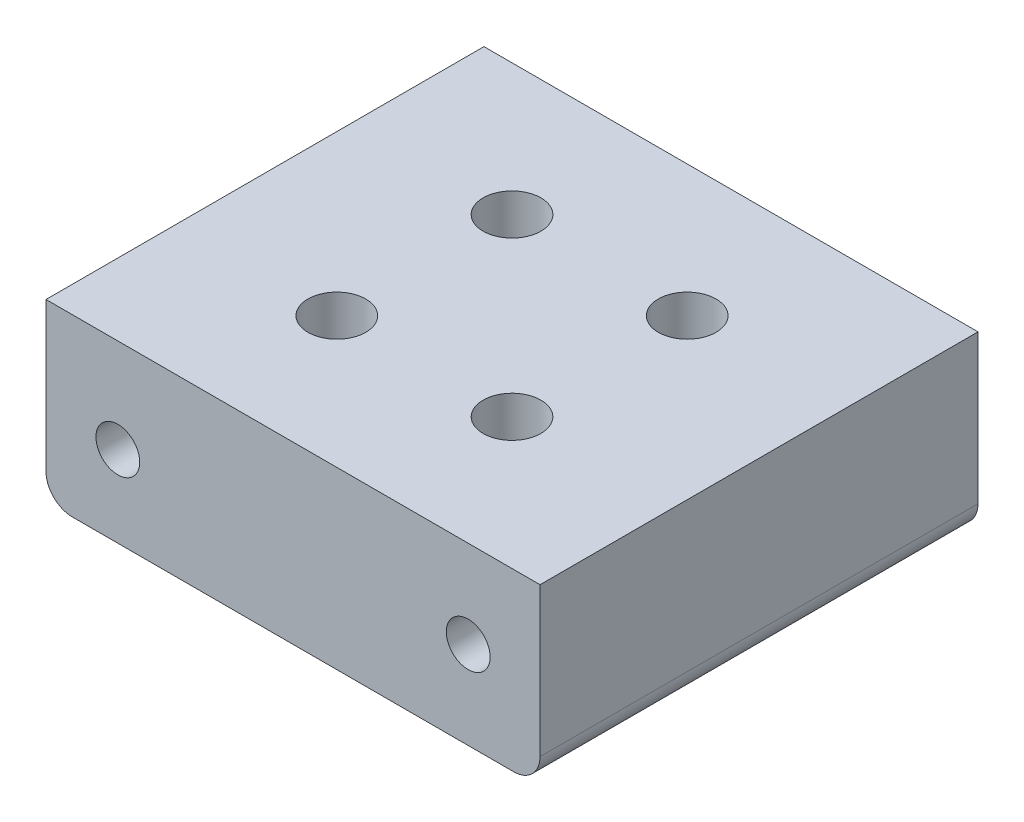
SolidWorks part; units mm, degrees
ref_plane "Front Plane" through (0, 0, 0) normal (0, 0, 1) x (1, 0, 0)
ref_plane "Top Plane" through (0, 0, 0) normal (0, 1, 0) x (1, 0, 0)
ref_plane "Right Plane" through (0, 0, 0) normal (1, 0, 0) x (0, 0, -1)
sketch "Sketch1" plane through (0, 0, 0) normal (0, 0, 1) x (1, 0, 0)
  line L5 (28.2, -17.5) -> (-28.2, -17.5)
  line L8 (-25.2, -37.5) -> (25.2, -37.5)
  line L9 (28.2, -34.5) -> (28.2, -17.5)
  line L11 (-28.2, -17.5) -> (-28.2, -34.5)
  arc A8 (25.2, -37.5) -> (28.2, -34.5) centre (25.2, -34.5) ccw
  arc A11 (-28.2, -34.5) -> (-25.2, -37.5) centre (-25.2, -34.5) ccw
extrude "Boss-Extrude1" add sketch "Sketch1" along normal blind 50
hole_wizard "Tap Drill for M6 Tap1" positions "Sketch2" profile "Sketch3" hole size "M6" standard "ISO" end condition through all
sketch "Sketch2" plane through (0, 0, 0) normal (0, 0, -1) x (-1, 0, 0)
  point P0 (-20, -27.5)
  point P2 (20, -28.2377)
sketch "Sketch3" plane through (20, -27.5, 0) normal (1, 0, 0) x (0, 1, 0)
  line L0 (0, 0) -> (0, 50)
  line L1 (0, 50) -> (2.5, 50)
  line L2 (2.5, 50) -> (2.5, 0)
  line L5 (2.5, 0) -> (0, 0)
  line L11 (0, -6.35) -> (0, 107.95) construction
  dimension "Thru Hole Dia." = 5
  dimension "Thru Hole Depth" = 50
hole_wizard "M6 Clearance Hole1" positions "Sketch5" profile "Sketch4" hole size "M6" standard "ISO" end condition through all
sketch "Sketch5" plane through (0, -37.5, 0) normal (0, -1, 0) x (-1, 0, 0)
  line L1 (10, -15) -> (-10, -15)
  line L2 (10, -15) -> (10, -35)
  line L3 (10, -35) -> (-10, -35)
  line L4 (-10, -15) -> (-10, -35)
  line L6 (25.2, -25) -> (-25.2, -25)
  line L8 (0, -50) -> (0, 0)
  point P2 (10, -15)
  point P3 (-10, -35)
  point P24 (10, -35)
  point P25 (-10, -15)
  dimension "D1" = 20
  dimension "D2" = 20
  dimension "D3" = 10
  dimension "D4" = 10
sketch "Sketch4" plane through (-10, -37.5, 15) normal (1, 0, 0) x (0, 0, -1)
  line L0 (0, 0) -> (0, 20)
  line L1 (0, 20) -> (3.3, 20)
  line L2 (3.3, 20) -> (3.3, 0)
  line L5 (3.3, 0) -> (0, 0)
  line L11 (0, -6.35) -> (0, 107.95) construction
  dimension "Thru Hole Dia." = 6.6
  dimension "Thru Hole Depth" = 20
